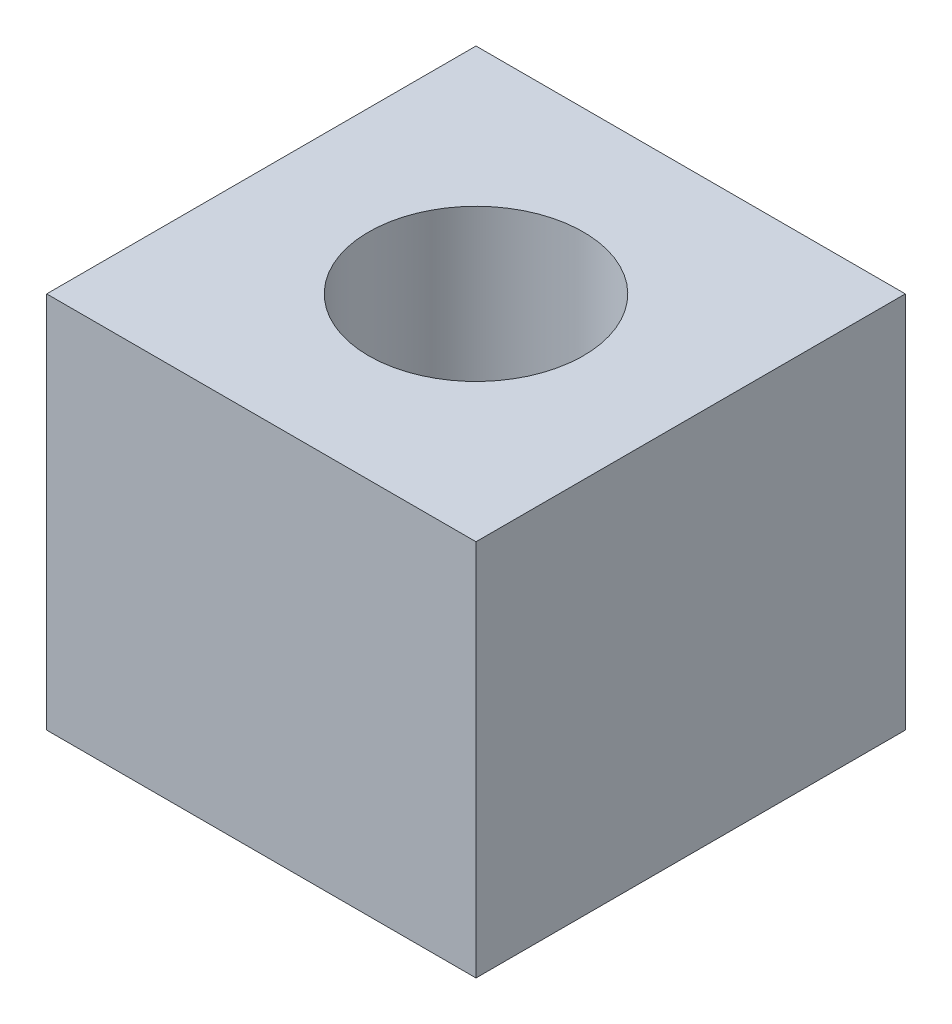
SolidWorks part; units mm, degrees
ref_plane "Front Plane" through (0, 0, 0) normal (0, 0, 1) x (1, 0, 0)
ref_plane "Top Plane" through (0, 0, 0) normal (0, 1, 0) x (1, 0, 0)
ref_plane "Right Plane" through (0, 0, 0) normal (1, 0, 0) x (0, 0, -1)
sketch "Sketch1" plane through (0, 0, 0) normal (0, 1, 0) x (1, 0, 0)
  line L1 (12.7, -12.7) -> (-12.7, -12.7)
  line L2 (12.7, -12.7) -> (12.7, 12.7)
  line L3 (12.7, 12.7) -> (-12.7, 12.7)
  line L4 (-12.7, -12.7) -> (-12.7, 12.7)
  line L5 (12.7, -12.7) -> (-12.7, 12.7) construction
  line L6 (12.7, 12.7) -> (-12.7, -12.7) construction
  point P0 (0, 0)
  dimension "D1" = 25.4
  dimension "D2" = 25.4
extrude "Boss-Extrude1" add sketch "Sketch1" along normal blind 22.352
sketch "Sketch2" plane through (0, 22.352, 0) normal (0, 1, 0) x (1, 0, 0)
  circle A0 centre (0, 0) radius 6.35
  dimension "D1" = 12.7
extrude "Cut-Extrude1" cut sketch "Sketch2" against normal blind 25.4
